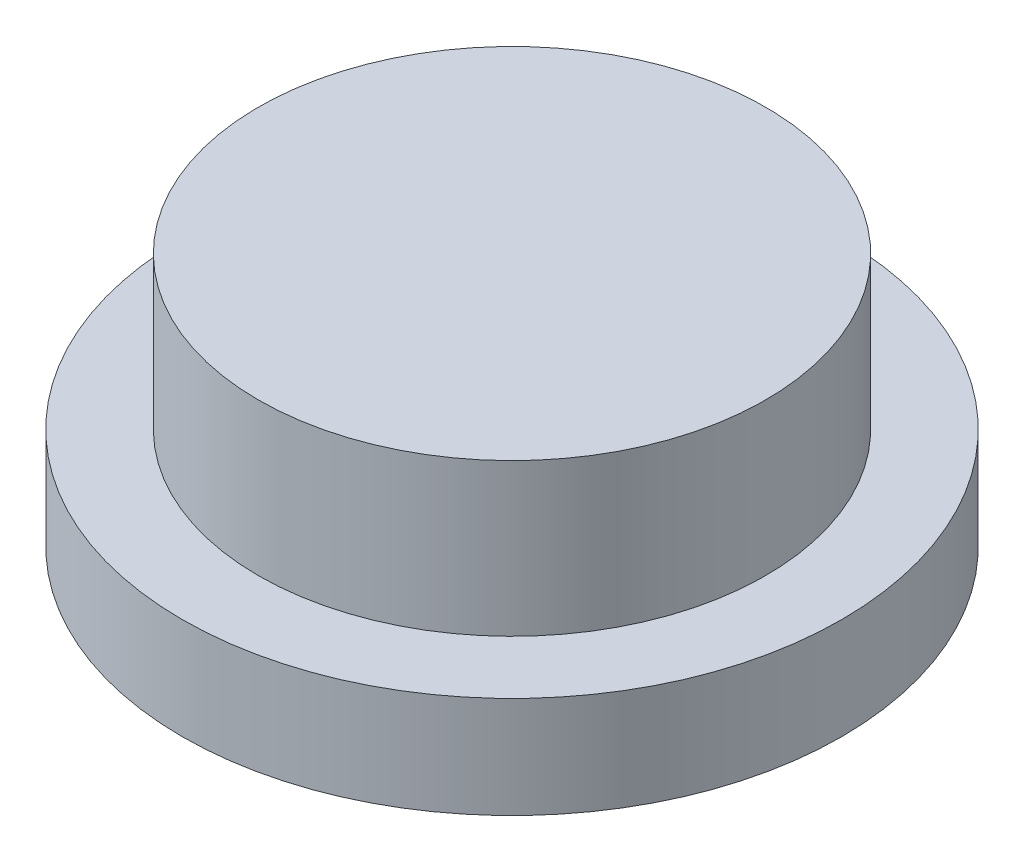
SolidWorks part; units mm, degrees
ref_plane "Спереди" through (0, 0, 0) normal (0, 0, 1) x (1, 0, 0)
ref_plane "Сверху" through (0, 0, 0) normal (0, 1, 0) x (1, 0, 0)
ref_plane "Справа" through (0, 0, 0) normal (1, 0, 0) x (0, 0, -1)
sketch "Эскиз1" plane through (0, 0, 0) normal (1, 0, 0) x (0, 0, -1)
  line L0 (0, 57.5393) -> (0, -39.369) construction
  line L1 (0, 10) -> (10, 10)
  line L2 (10, 10) -> (10, 4)
  line L3 (10, 4) -> (13, 4)
  line L4 (13, 4) -> (13, 0)
  line L5 (13, 0) -> (0, 0)
  line L6 (0, 10) -> (0, 0)
  point P5 (0, 0)
  point P10 (0, 0)
  point P11 (0, 0)
revolve "Повернуть1" add sketch "Эскиз1" angle 360 about L0
